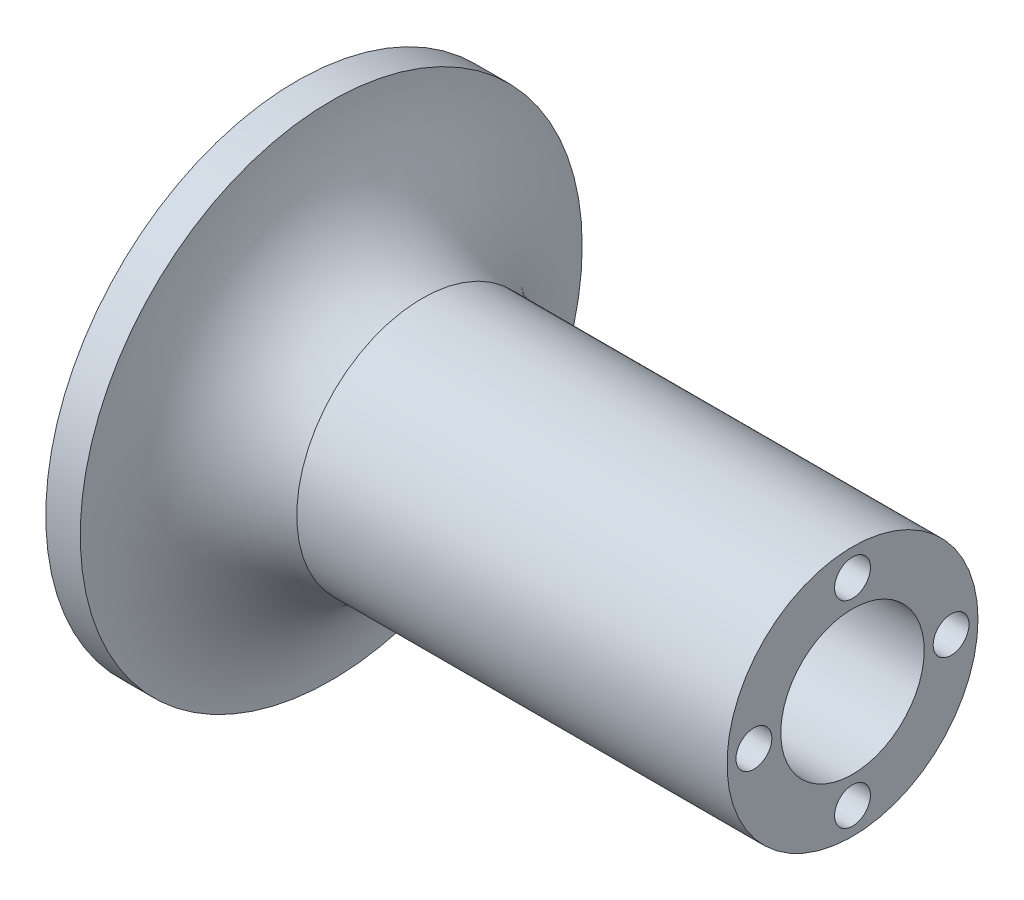
SolidWorks part; units mm, degrees
ref_plane "Plano frontal" through (0, 0, 0) normal (0, 0, 1) x (1, 0, 0)
ref_plane "Plano superior" through (0, 0, 0) normal (0, 1, 0) x (1, 0, 0)
ref_plane "Plano direito" through (0, 0, 0) normal (1, 0, 0) x (0, 0, -1)
sketch "Esboço1" plane through (0, 0, 0) normal (0, 0, 1) x (1, 0, 0)
  line L0 (-67.0201, 0) -> (-94.0101, 0)
  line L1 (-59.0101, 35) -> (60.9899, 35)
  line L2 (-67.0201, 0) -> (60.9899, 0)
  line L3 (60.9899, 0) -> (60.9899, 35)
  line L4 (-67.0201, 0) -> (-149.8469, 0) construction
  line L5 (-149.8469, 0) -> (130.4621, 0) construction
  line L6 (-84.3919, 70) -> (-94.0101, 70)
  line L7 (-94.0101, 70) -> (-94.0101, 0)
  arc A0 (-84.3919, 70) -> (-59.0101, 35) centre (-47.5696, 70) ccw
  dimension "D1" = 35
  dimension "D2" = 70
  dimension "D3" = 120
  dimension "D4" = 35
revolve "Revolução1" add sketch "Esboço1" angle 360 about L4
sketch "Esboço8" plane through (60.9899, 0, 0) normal (1, 0, 0) x (0, 0, -1)
  circle A0 centre (0, 0) radius 20
extrude "Corte-extrusão1" cut sketch "Esboço8" against normal blind 140
sketch "Esboço9" plane through (60.9899, 0, 0) normal (1, 0, 0) x (0, 0, -1)
  circle A4 centre (0, 27.5) radius 5
  circle A5 centre (27.5, 0) radius 5
  circle A6 centre (-27.5, 0) radius 5
  circle A7 centre (0, -27.5) radius 5
  point P11 (0, 27.5)
  dimension "D1" = 10
  dimension "D2" = 10
  dimension "D3" = 10
  dimension "D4" = 10
extrude "Corte-extrusão2" cut sketch "Esboço9" against normal blind 20
